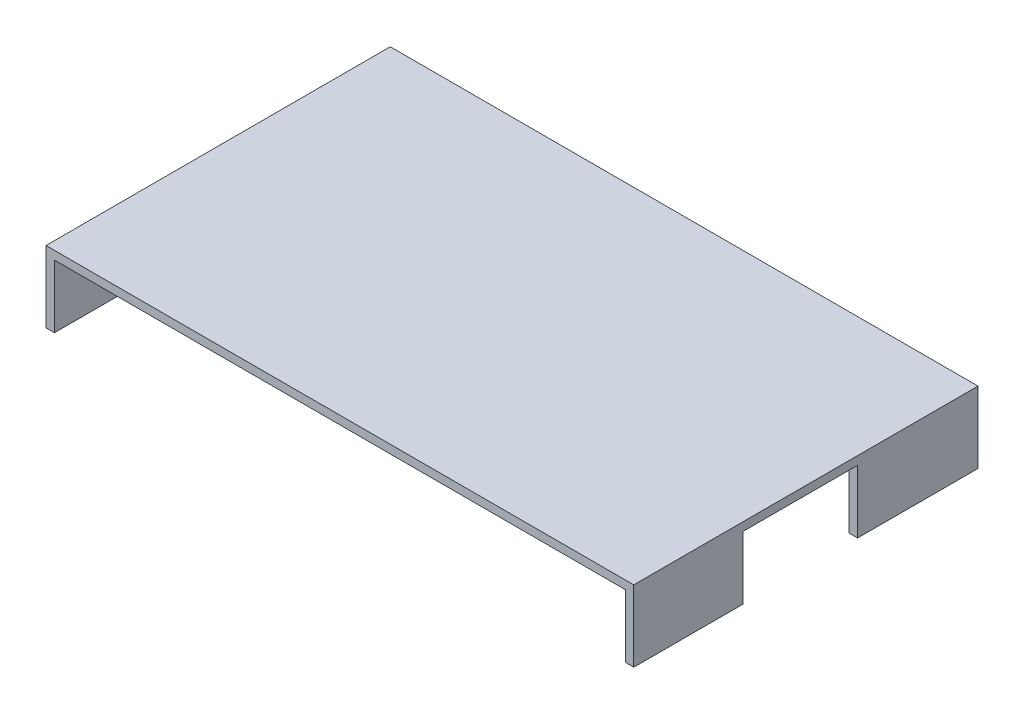
SolidWorks part; units mm, degrees
ref_plane "前视基准面" through (0, 0, 0) normal (0, 0, 1) x (1, 0, 0)
ref_plane "上视基准面" through (0, 0, 0) normal (0, 1, 0) x (1, 0, 0)
ref_plane "右视基准面" through (0, 0, 0) normal (1, 0, 0) x (0, 0, -1)
sketch "草图1" plane through (0, 0, 0) normal (0, 1, 0) x (1, 0, 0)
  line L0 (0, -41) -> (70, -41)
  line L1 (0, 41) -> (-70, 41)
  line L2 (-70, 41) -> (-70, 0)
  line L3 (0, 41) -> (70, 41)
  line L4 (70, 41) -> (70, -6.0176)
  line L5 (70, -41) -> (70, -6.0176)
  line L6 (0, -41) -> (-70, -41)
  line L7 (-70, -41) -> (-70, 0)
extrude "凸台-拉伸1" add sketch "草图1" along normal blind 2
sketch "草图2" plane through (0, 0, 0) normal (0, -1, 0) x (1, 0, 0)
  line L0 (-70, -41) -> (-68, -41)
  line L1 (70, -41) -> (-70, -41) construction
  line L2 (-68, -41) -> (-68, 41)
  line L3 (-70, 41) -> (70, 41) construction
  line L4 (-68, 41) -> (-70, 41)
  line L5 (-70, 41) -> (-70, -41)
  line L6 (70, -41) -> (68, -41)
  line L7 (68, -41) -> (68, 41)
  line L8 (68, 41) -> (70, 41)
  line L9 (70, 41) -> (70, -41)
extrude "凸台-拉伸2" add sketch "草图2" along normal blind 15
sketch "草图4" plane through (70, 0, 0) normal (1, 0, 0) x (0, 0, -1)
  line L0 (0, 0) -> (-14.99, 0)
  line L1 (0, 0) -> (12.32, 0)
  line L2 (12.32, 0) -> (12.32, -15)
  line L3 (41, -15) -> (-41, -15) construction
  line L4 (-14.99, 0) -> (-14.99, -15)
  line L5 (-14.99, -15) -> (12.32, -15)
extrude "切除-拉伸2" cut sketch "草图4" against normal blind 20
